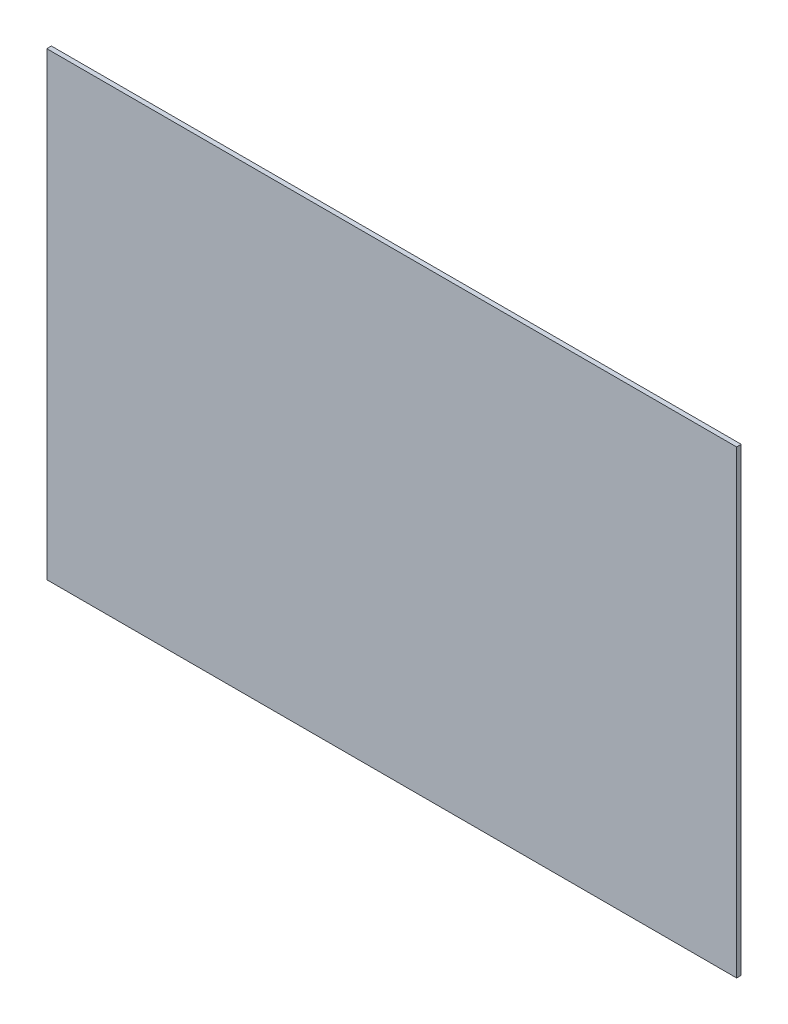
SolidWorks part; units mm, degrees
material "Plain Carbon Steel"
ref_plane "Front Plane" through (0, 0, 0) normal (0, 0, 1) x (1, 0, 0)
ref_plane "Top Plane" through (0, 0, 0) normal (0, 1, 0) x (1, 0, 0)
ref_plane "Right Plane" through (0, 0, 0) normal (1, 0, 0) x (0, 0, -1)
sketch "Sketch1" plane through (0, 0, 0) normal (0, 0, 1) x (1, 0, 0)
  line L1 (150, 100) -> (-150, 100)
  line L2 (150, 100) -> (150, -100)
  line L3 (150, -100) -> (-150, -100)
  line L4 (-150, 100) -> (-150, -100)
  line L5 (150, 100) -> (-150, -100) construction
  line L6 (150, -100) -> (-150, 100) construction
  point P0 (0, 0)
  dimension "D1" = 300
  dimension "D2" = 200
extrude "Boss-Extrude1" add sketch "Sketch1" along normal blind 2
